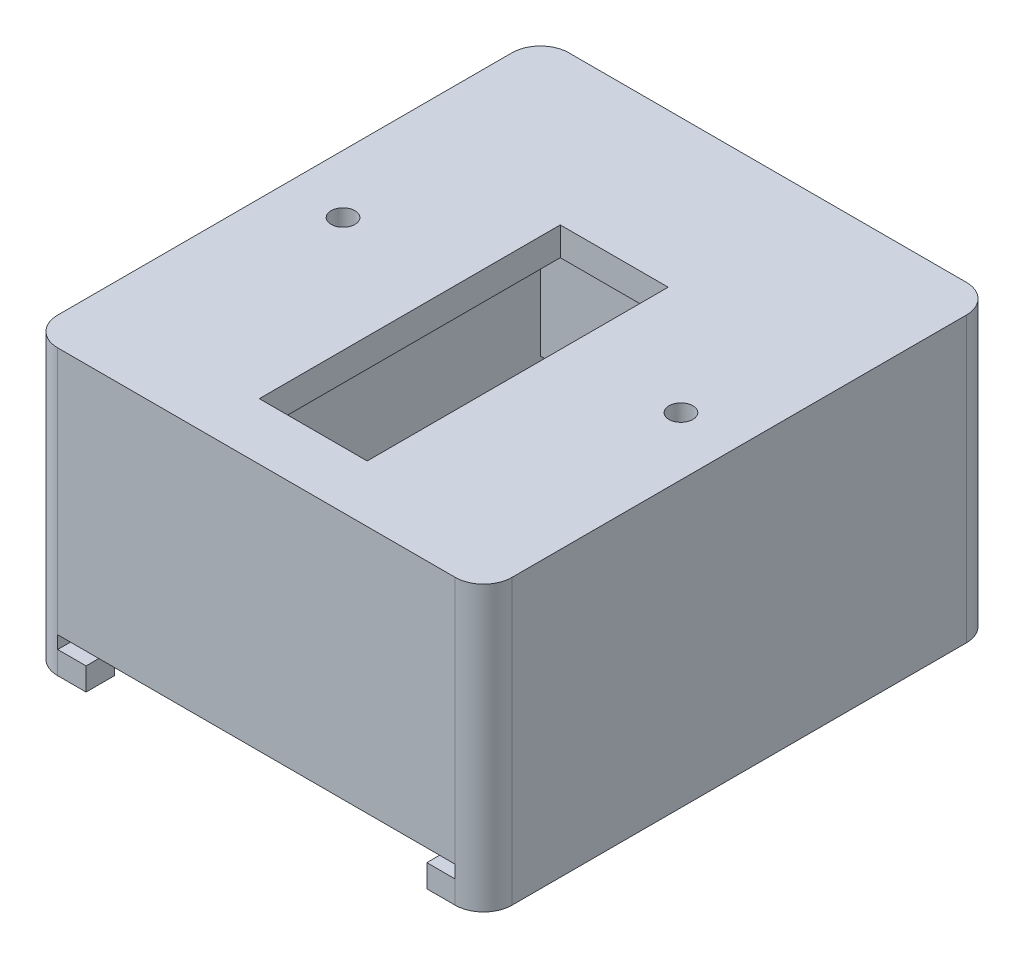
SolidWorks part; units mm, degrees
ref_plane "Front Plane" through (0, 0, 0) normal (0, 0, 1) x (1, 0, 0)
ref_plane "Top Plane" through (0, 0, 0) normal (0, 1, 0) x (1, 0, 0)
ref_plane "Right Plane" through (0, 0, 0) normal (1, 0, 0) x (0, 0, -1)
sketch "Sketch1" plane through (0, 0, 0) normal (0, 1, 0) x (1, 0, 0)
  line L1 (-40, 45) -> (40, 45)
  line L2 (-40, 45) -> (-40, -45)
  line L3 (-40, -45) -> (40, -45)
  line L4 (40, 45) -> (40, -45)
  line L5 (-40, 45) -> (40, -45) construction
  line L6 (-40, -45) -> (40, 45) construction
  line L7 (-9.5, 18) -> (9.5, 18)
  line L8 (-9.5, 18) -> (-9.5, -35)
  line L9 (-9.5, -35) -> (9.5, -35)
  line L10 (9.5, 18) -> (9.5, -35)
  line L11 (-9.5, 18) -> (9.5, -35) construction
  line L12 (-9.5, -35) -> (9.5, 18) construction
  circle A0 centre (29.75, 0) radius 2.1
  circle A1 centre (-29.75, 0) radius 2.1
  point P0 (0, 0)
  point P6 (0, -8.5)
  point P15 (40, 0)
  dimension "D7" = 10.25
  dimension "D8" = 4.2
  dimension "D10" = 4.2
  dimension "D11" = 45
  dimension "D12" = 45
  dimension "D1" = 80
  dimension "D2" = 90
  dimension "D3" = 10
  dimension "D4" = 53
  dimension "D5" = 30.5
  dimension "D6" = 19
  dimension "D9" = 10.25
extrude "Boss-Extrude3" add sketch "Sketch1" along normal blind 50
sketch "Sketch5" plane through (0, 0, 0) normal (0, -1, 0) x (-1, 0, 0)
  line L1 (35, -40) -> (-35, -40)
  line L2 (35, -40) -> (35, 40)
  line L3 (35, 40) -> (-35, 40)
  line L4 (-35, -40) -> (-35, 40)
  line L5 (35, -40) -> (-35, 40) construction
  line L6 (35, 40) -> (-35, -40) construction
  point P0 (0, 0)
  dimension "D1" = 70
  dimension "D2" = 80
extrude "Cut-Extrude2" cut sketch "Sketch5" against normal blind 45
sketch "Sketch6" plane through (0, 0, -45) normal (0, 0, -1) x (-1, 0, 0)
  line L0 (-40, 50) -> (-40, 0) construction
  line L1 (-40, 0) -> (40, 0) construction
  circle A0 centre (-5, 40) radius 2.5
  circle A1 centre (5, 40) radius 2.5
  dimension "D1" = 5
  dimension "D5" = 5
  dimension "D2" = 40
  dimension "D3" = 35
  dimension "D4" = 10
  dimension "D6" = 40
extrude "Cut-Extrude5" cut sketch "Sketch6" against normal blind 10.25
sketch "Sketch7" plane through (-40, 0, 0) normal (-1, 0, 0) x (0, 0, 1)
  line L0 (0, -27.5) -> (0, 27.5) construction
  line L1 (-26.3756, 31) -> (-22.3342, 38)
  line L2 (-22.3342, 38) -> (-26.3756, 45)
  line L3 (-26.3756, 45) -> (-34.4585, 45)
  line L4 (-34.4585, 45) -> (-38.5, 38)
  line L5 (-38.5, 38) -> (-34.4585, 31)
  line L6 (-34.4585, 31) -> (-26.3756, 31)
  line L7 (-45, 50) -> (45, 50) construction
  line L8 (-45, 50) -> (-45, 0) construction
  line L15 (34.4585, 31) -> (26.3756, 31)
  line L16 (38.5, 38) -> (34.4585, 31)
  line L17 (34.4585, 45) -> (38.5, 38)
  line L18 (26.3756, 45) -> (34.4585, 45)
  line L19 (22.3342, 38) -> (26.3756, 45)
  line L20 (26.3756, 31) -> (22.3342, 38)
  circle A0 centre (-30.4171, 38) radius 7 construction
  circle A2 centre (30.4171, 38) radius 7 construction
  dimension "D1" = 14
  dimension "D2" = 5
  dimension "D3" = 6.5
extrude "Cut-Extrude6" cut sketch "Sketch7" against normal blind 10.25
fillet "Fillet2" radius 5 4 edges at (40, 25, 45) (-40, 25, -45) (40, 25, -45) (-40, 25, 45)
sketch "Sketch8" plane through (0, 0, 45) normal (0, 0, 1) x (1, 0, 0)
  line L0 (35, 0) -> (35, 50) construction
  line L1 (-35, 6.2487) -> (35, 6.2487)
  line L2 (-35, 6.2487) -> (-35, 4)
  line L3 (-35, 4) -> (-30, 4)
  line L4 (35, 6.2487) -> (35, 4)
  line L5 (-35, 6.2487) -> (35, 4) construction
  line L6 (-35, 4) -> (35, 6.2487) construction
  line L7 (-35, 50) -> (-35, 0) construction
  line L8 (-35, 0) -> (35, 0) construction
  line L9 (-30, 4) -> (-30, 0)
  line L10 (30, 0) -> (30, 4)
  line L11 (30, 4) -> (35, 4)
  line L12 (-30, 0) -> (30, 0)
  point P0 (0, 5.1243)
  point P5 (35, 5.1243)
  dimension "D1" = 0
  dimension "D2" = 0
  dimension "D3" = 4
  dimension "D4" = 2.2487
  dimension "D5" = 5
  dimension "D6" = 5
  dimension "D7" = 6.2487
extrude "Cut-Extrude9" cut sketch "Sketch8" against normal blind 1000
